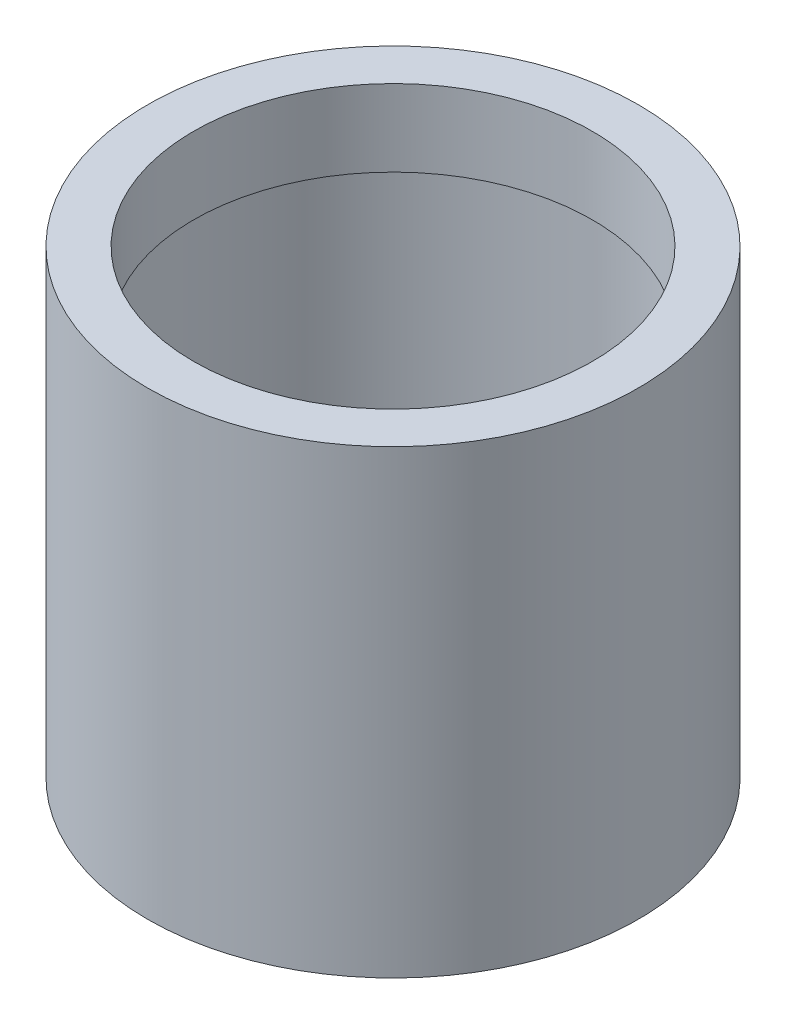
SolidWorks part; units mm, degrees
material "1060 Alloy"
ref_plane "Front Plane" through (0, 0, 0) normal (0, 0, 1) x (1, 0, 0)
ref_plane "Top Plane" through (0, 0, 0) normal (0, 1, 0) x (1, 0, 0)
ref_plane "Right Plane" through (0, 0, 0) normal (1, 0, 0) x (0, 0, -1)
sketch "Sketch1" plane through (0, 0, 0) normal (0, 1, 0) x (1, 0, 0)
  circle A0 centre (0, 0) radius 16
  circle A1 centre (0, 0) radius 14.5
  dimension "D1" = 32
  dimension "D2" = 29
extrude "Boss-Extrude1" add sketch "Sketch1" along normal blind 25
sketch "Sketch2" plane through (0, 25, 0) normal (0, 1, 0) x (1, 0, 0)
  circle A0 centre (0, 0) radius 16
  circle A1 centre (0, 0) radius 13
  dimension "D1" = 26
extrude "Boss-Extrude2" add sketch "Sketch2" along normal blind 5
